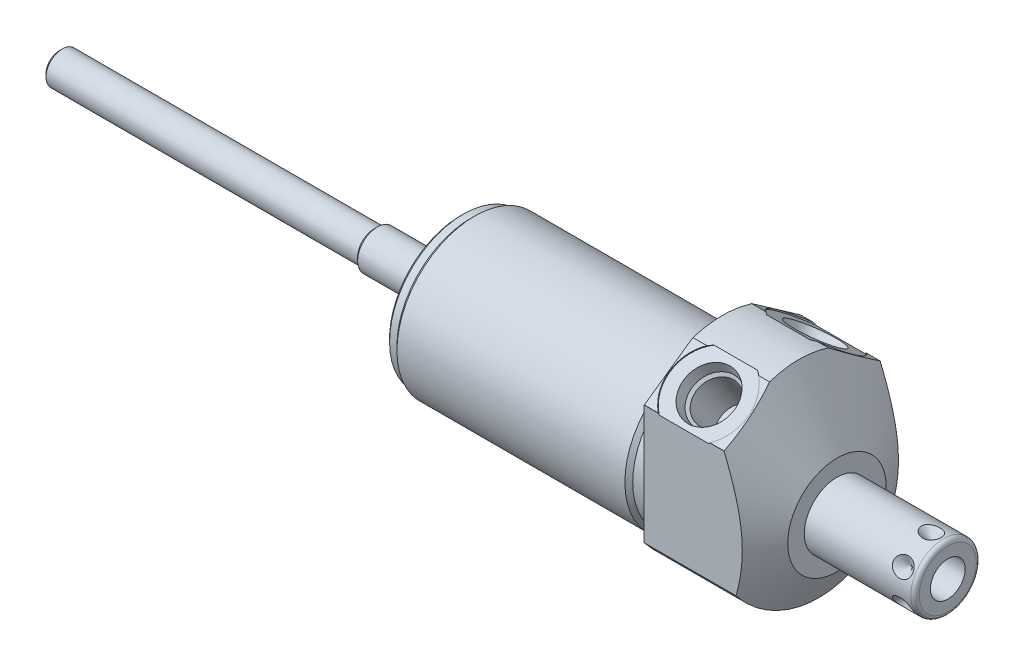
SolidWorks part; units mm, degrees
material "Alloy Steel"
ref_plane "Front Plane" through (0, 0, 0) normal (0, 0, 1) x (1, 0, 0)
ref_plane "Top Plane" through (0, 0, 0) normal (0, 1, 0) x (1, 0, 0)
ref_plane "Right Plane" through (0, 0, 0) normal (1, 0, 0) x (0, 0, -1)
ref_plane "Plane1" through (0, 0, 0) normal (1, 0, 0) x (0, 0, -1)
sketch "Sketch1" plane through (0, 0, 0) normal (1, 0, 0) x (0, 0, -1)
  circle A0 centre (0, 0) radius 23.8125
  dimension "D1" = 47.625
extrude "Extrude1" add sketch "Sketch1" along normal blind 27.7876 and the other way blind 63.5
ref_plane "Plane2" through (0, 0, 0) normal (1, 0, 0) x (0, 0, -1)
sketch "Sketch2" plane through (0, 0, 0) normal (1, 0, 0) x (0, 0, -1)
  line L0 (-20.7455, -4.191) -> (20.7455, -4.191) construction
  circle A0 centre (0, -4.191) radius 18.8595
  circle A1 centre (0, 0) radius 23.8125 construction
  circle A2 centre (0, 0) radius 23.8125
  dimension "D2" = 37.719
  dimension "D1" = 4.191
extrude "Cut-Extrude1" cut sketch "Sketch2" against normal up to next
ref_plane "Plane4" through (0, 0, 0) normal (-1, 0, 0) x (0, 0, 1)
sketch "Sketch4" plane through (0, 0, 0) normal (-1, 0, 0) x (0, 0, 1)
  line L0 (18.923, -14.4553) -> (18.923, 14.4659)
  line L1 (18.923, 14.4659) -> (0, 27.7159)
  line L2 (-18.923, -14.4553) -> (-18.923, 14.4659)
  line L3 (-18.923, 14.4659) -> (0, 27.7159)
  line L4 (0, -26.3889) -> (0, 30.2923) construction
  circle A0 centre (0, 0) radius 28.575
  circle A1 centre (0, 0) radius 23.8125 construction
  arc A3 (-18.923, -14.4553) -> (18.923, -14.4553) centre (0, 0) ccw
  dimension "D4" = 57.15
  dimension "D1" = 37.846
  dimension "D2" = 27.7159
  dimension "D3" = 55
extrude "Cut-Extrude3" cut sketch "Sketch4" against normal up to next
ref_plane "Plane6" through (0, 0, 0) normal (0, 0, 1) x (1, 0, 0)
sketch "Sketch6" plane through (0, 0, 0) normal (0, 0, 1) x (1, 0, 0)
  line L0 (4.764, 47.625) -> (27.7876, 7.747)
  line L1 (3.6128, -4.191) -> (28.9388, -4.191) construction
  line L2 (-63.5, -4.191) -> (0, -4.191) construction
  line L3 (27.7876, 7.747) -> (27.7876, 47.625)
  line L4 (27.7876, 47.625) -> (4.764, 47.625)
  line L5 (27.7876, -14.4553) -> (27.7876, 14.4553) construction
  dimension "D1" = 23.876
  dimension "D2" = 30
  dimension "D3" = 39.878
revolve "Cut-Revolve2" cut sketch "Sketch6" angle 360 about L1
ref_plane "Plane7" through (9.652, 18.3948, 12.869) normal (1, 0, 0) x (0, 0.5736, -0.8192)
sketch "S2D0002" plane through (9.652, 18.3948, 12.869) normal (1, 0, 0) x (0, 0.5736, -0.8192)
  line L0 (0, 0) -> (6.1849, 0)
  line L1 (6.1849, 0) -> (5.6423, -2.5527)
  line L2 (5.6423, -2.5527) -> (4.9784, -3.2166)
  line L3 (4.9784, -3.2166) -> (4.9784, -13.462)
  line L4 (4.9784, -13.462) -> (0, -13.462)
  line L5 (0, -13.462) -> (0, 0)
  line L6 (0, -14.1351) -> (0, 0.6731) construction
  dimension "D1" = 13.462
revolve "Cut-Revolve3" cut sketch "S2D0002" angle 360 about L6
ref_plane "Plane8" through (9.652, 18.3948, -12.869) normal (1, 0, 0) x (0, -0.5736, -0.8192)
sketch "Sketch8" plane through (9.652, 18.3948, -12.869) normal (1, 0, 0) x (0, -0.5736, -0.8192)
  line L0 (0, 0) -> (6.1849, 0)
  line L1 (6.1849, 0) -> (5.6423, -2.5527)
  line L2 (5.6423, -2.5527) -> (4.9784, -3.2166)
  line L3 (4.9784, -3.2166) -> (4.9784, -13.462)
  line L4 (4.9784, -13.462) -> (0, -13.462)
  line L5 (0, -13.462) -> (0, 0)
  line L6 (0, -14.1351) -> (0, 0.6731) construction
  dimension "D1" = 13.462
revolve "Cut-Revolve4" cut sketch "Sketch8" angle 360 about L6
sketch "Sketch18" plane through (0, 18.5976, 13.0222) normal (0, 0.8192, 0.5736) x (1, 0, 0)
  circle A0 centre (9.652, 0.0091) radius 9.525
  dimension "D1" = 19.05
extrude "Cut-Extrude4" cut sketch "Sketch18" against normal blind 0.254
sketch "Sketch19" plane through (0, 18.5976, -13.0222) normal (0, 0.8192, -0.5736) x (1, 0, 0)
  circle A0 centre (9.652, -0.0091) radius 9.525
  dimension "D1" = 19.05
extrude "Cut-Extrude5" cut sketch "Sketch19" against normal blind 0.254
ref_plane "Plane10" through (0, 0, 0) normal (0, 0, 1) x (1, 0, 0)
sketch "Sketch10" plane through (0, 0, 0) normal (0, 0, 1) x (1, 0, 0)
  line L0 (0, 14.6685) -> (0, 13.716)
  line L1 (0, 13.716) -> (-3.81, 13.716)
  line L2 (-3.81, 13.716) -> (-4.7625, 14.6685)
  line L3 (-5.0006, -4.191) -> (0.2381, -4.191) construction
  line L4 (0, 14.6685) -> (-4.7625, 14.6685)
  line L5 (-63.5, -4.191) -> (0, -4.191) construction
  line L6 (0, 14.6685) -> (-63.5, 14.6685) construction
  line L7 (0, 14.6685) -> (0, -23.0505) construction
  dimension "D1" = 35.814
  dimension "D2" = 3.81
  dimension "D3" = 45
revolve "Cut-Revolve6" cut sketch "Sketch10" angle 360 about L3
ref_plane "Plane12" through (0, 0, 0) normal (0, 0, 1) x (1, 0, 0)
sketch "Sketch12" plane through (0, 0, 0) normal (0, 0, 1) x (1, 0, 0)
  line L0 (-63.5, 14.6685) -> (-63.5, 13.716)
  line L1 (-63.5, 13.716) -> (-60.96, 13.716)
  line L2 (-60.96, 13.716) -> (-60.0075, 14.6685)
  line L3 (-63.6746, -4.191) -> (-59.8329, -4.191) construction
  line L4 (-63.5, 14.6685) -> (-60.0075, 14.6685)
  line L6 (-63.5, -4.191) -> (-4.7625, -4.191) construction
  line L7 (-4.7625, 14.6685) -> (-63.5, 14.6685) construction
  line L8 (-63.5, 14.6685) -> (-63.5, -23.0505) construction
  dimension "D1" = 35.814
  dimension "D2" = 2.54
  dimension "D3" = 45
revolve "Cut-Revolve8" cut sketch "Sketch12" angle 360 about L3
chamfer "Chamfer1" distance 0.762 angle 45 1 edges at (-63.5, -4.191, 17.907)
ref_plane "Plane13" through (0, 0, 0) normal (0, 0, 1) x (0, -1, 0)
sketch "Sketch13" plane through (0, 0, 0) normal (0, 0, 1) x (0, -1, 0)
  line L0 (4.191, 27.7876) -> (4.191, 54.6354)
  line L1 (4.191, 54.6354) -> (11.1125, 54.6354)
  line L2 (12.1285, 53.6194) -> (12.1285, 27.7876)
  line L3 (12.1285, 27.7876) -> (4.191, 27.7876)
  line L4 (4.191, 26.4452) -> (4.191, 55.9778) construction
  line L5 (4.191, -60.0075) -> (4.191, -4.7625) construction
  line L6 (16.129, 27.7876) -> (-7.747, 27.7876) construction
  line L7 (14.4553, 0) -> (-14.4553, 0) construction
  arc A0 (12.1285, 53.6194) -> (11.1125, 54.6354) centre (11.1125, 53.6194) ccw
  dimension "D2" = 1.016
  dimension "D1" = 54.6354
  dimension "D3" = 15.875
revolve "Revolve1" add sketch "Sketch13" angle 360 about L4
ref_plane "Plane14" through (54.6354, -8.4074, 0) normal (0, 0, 1) x (0, -1, 0)
sketch "S2D0001" plane through (54.6354, -8.4074, 0) normal (0, 0, 1) x (0, -1, 0)
  line L0 (0, 0) -> (0, -15.24)
  line L1 (0, -15.24) -> (-4.2164, -17.7735)
  line L2 (0, 0) -> (-4.2164, 0)
  line L3 (-4.2164, 0) -> (-4.2164, -17.7735)
  line L4 (-4.2164, -18.6621) -> (-4.2164, 0.8887) construction
  line L5 (-4.2164, -1.016) -> (-4.2164, -26.8478) construction
  line L6 (2.7051, 0) -> (-11.1379, 0) construction
  dimension "D1" = 8.4328
  dimension "D2" = 15.24
  dimension "D3" = 59
revolve "Cut-Revolve9" cut sketch "S2D0001" angle 360 about L4
ref_plane "Plane16" through (50.673, -12.1285, 0) normal (0, 0, 1) x (-1, 0, 0)
ref_plane "Plane17" through (0, -3.1433, -1.8148) normal (0, 0.866, 0.5) x (-1, 0, 0)
sketch "Sketch16" plane through (50.673, 3.7465, 0) normal (0, 0, -1) x (-1, 0, 0)
  line L0 (0, 0) -> (2.413, 0)
  line L1 (2.413, 0) -> (0, -2.413)
  line L2 (0, 0) -> (0, -2.413)
  line L3 (0, -5.071) -> (0, 0.1207) construction
  line L4 (-3.9624, -1.016) -> (-3.9624, -14.859) construction
  line L5 (22.8854, 0) -> (-2.9464, 0) construction
  dimension "D1" = 3.9624
  dimension "D2" = 4.826
  dimension "D3" = 45
revolve "Cut-Revolve10" cut sketch "Sketch16" angle 360 about L3
pattern_circular "CirPattern1" count 6 over 360 about axis through (26.4452, -4.191, 0) along (-1, 0, 0) of "Cut-Revolve10"
sketch "Sketch20" plane through (-63.5, 0, 0) normal (-1, 0, 0) x (0, 0, 1)
  line L0 (0, -4.191) -> (28.7278, -4.191) construction
  circle A0 centre (0, -4.191) radius 15.875
  circle A1 centre (0, -4.191) radius 17.145 construction
  dimension "D1" = 31.75
extrude "Extrude2" add sketch "Sketch20" along normal blind 1.016
sketch "Sketch21" plane through (-64.516, 0, 0) normal (-1, 0, 0) x (0, 0, 1)
  line L0 (0, -4.191) -> (27.1956, -4.191) construction
  line L1 (8.6428, -2.9972) -> (15.83, -2.9972)
  line L2 (8.6428, -5.3848) -> (15.83, -5.3848)
  line L3 (0, -4.191) -> (0, -16.8471) construction
  line L4 (-8.6428, -5.3848) -> (-15.83, -5.3848)
  line L5 (-8.6428, -2.9972) -> (-15.83, -2.9972)
  arc A0 (8.6428, -2.9972) -> (-8.6428, -2.9972) centre (0, -4.191) ccw
  circle A1 centre (0, -4.191) radius 15.875 construction
  circle A2 centre (0, -4.191) radius 15.875 construction
  arc A3 (15.83, -5.3848) -> (15.83, -2.9972) centre (0, -4.191) ccw
  arc A4 (-15.83, -5.3848) -> (-15.83, -2.9972) centre (0, -4.191) cw
  arc A5 (-8.6428, -5.3848) -> (8.6428, -5.3848) centre (0, -4.191) ccw
  dimension "D1" = 17.4498
  dimension "D2" = 2.3876
extrude "Cut-Extrude6" cut sketch "Sketch21" against normal blind 1.524
sketch "Sketch22" plane through (-64.516, 0, 0) normal (-1, 0, 0) x (0, 0, 1)
  circle A0 centre (0, -4.191) radius 16.129
  circle A1 centre (0, -4.191) radius 15.875
  dimension "D1" = 32.258
  dimension "D2" = 31.75
extrude "Cut-Extrude7" cut sketch "Sketch22" against normal blind 2.54
sketch "Sketch23" plane through (0, 0, 0) normal (0, 0, 1) x (1, 0, 0)
  line L0 (-62.992, 0.5715) -> (-83.6168, 0.5715)
  line L2 (-83.6168, 0.5715) -> (-84.4169, -0.2286)
  line L3 (-84.4169, -0.2286) -> (-160.7058, -0.2286)
  line L4 (-160.7058, -0.2286) -> (-160.7058, -4.191)
  line L5 (-64.6874, -4.191) -> (-108.3313, -4.191) construction
  line L6 (-62.992, -4.191) -> (-64.516, -4.191) construction
  line L7 (-61.976, -4.191) -> (-63.5, -4.191) construction
  line L8 (54.6354, -11.1125) -> (54.6354, 2.7305) construction
  line L9 (-62.992, 0.5715) -> (-62.738, -4.191)
  line L10 (-62.738, 13.716) -> (-62.738, -22.098) construction
  line L11 (-62.738, -4.191) -> (-160.7058, -4.191)
  line L12 (-60.96, -4.191) -> (-62.738, -4.191) construction
  dimension "D1" = 215.3412
  dimension "D2" = 77.089
  dimension "D3" = 45
  dimension "D4" = 7.9248
  dimension "D5" = 9.525
revolve "Revolve2" add sketch "Sketch23" angle 360 about L5
chamfer "Chamfer2" distance 0.762 angle 45 3 edges at (-64.516, -20.066, 0) (-64.516, 11.684, 0) (-160.7058, -4.191, -3.9624)
